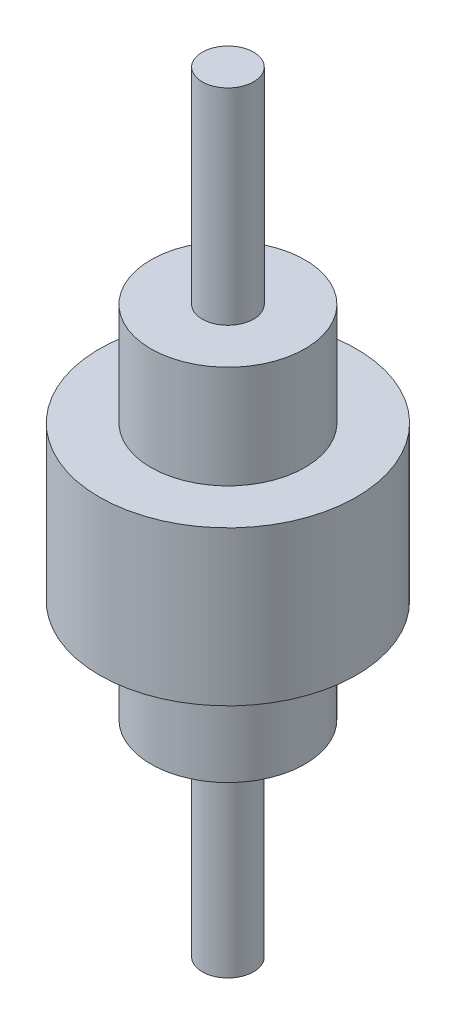
SolidWorks part; units mm, degrees
ref_plane "Front Plane" through (0, 0, 0) normal (0, 0, 1) x (1, 0, 0)
ref_plane "Top Plane" through (0, 0, 0) normal (0, 1, 0) x (1, 0, 0)
ref_plane "Right Plane" through (0, 0, 0) normal (1, 0, 0) x (0, 0, -1)
sketch "Sketch2" plane through (0, 0, 0) normal (0, 1, 0) x (1, 0, 0)
  circle A0 centre (0, 0) radius 50
extrude "Boss-Extrude1" add sketch "Sketch2" along normal blind 60
sketch "Sketch3" plane through (0, 60, 0) normal (0, 1, 0) x (1, 0, 0)
  circle A0 centre (0, 0) radius 30
extrude "Boss-Extrude2" add sketch "Sketch3" along normal blind 40
sketch "Sketch4" plane through (0, 100, 0) normal (0, 1, 0) x (1, 0, 0)
  circle A0 centre (0, 0) radius 10
extrude "Boss-Extrude3" add sketch "Sketch4" along normal blind 80
sketch "Sketch5" plane through (0, 0, 0) normal (0, -1, 0) x (1, 0, 0)
  circle A0 centre (0, 0) radius 30
extrude "Boss-Extrude4" add sketch "Sketch5" along normal blind 40
sketch "Sketch6" plane through (0, -40, 0) normal (0, -1, 0) x (1, 0, 0)
  circle A0 centre (0, 0) radius 10
extrude "Boss-Extrude5" add sketch "Sketch6" along normal blind 80
